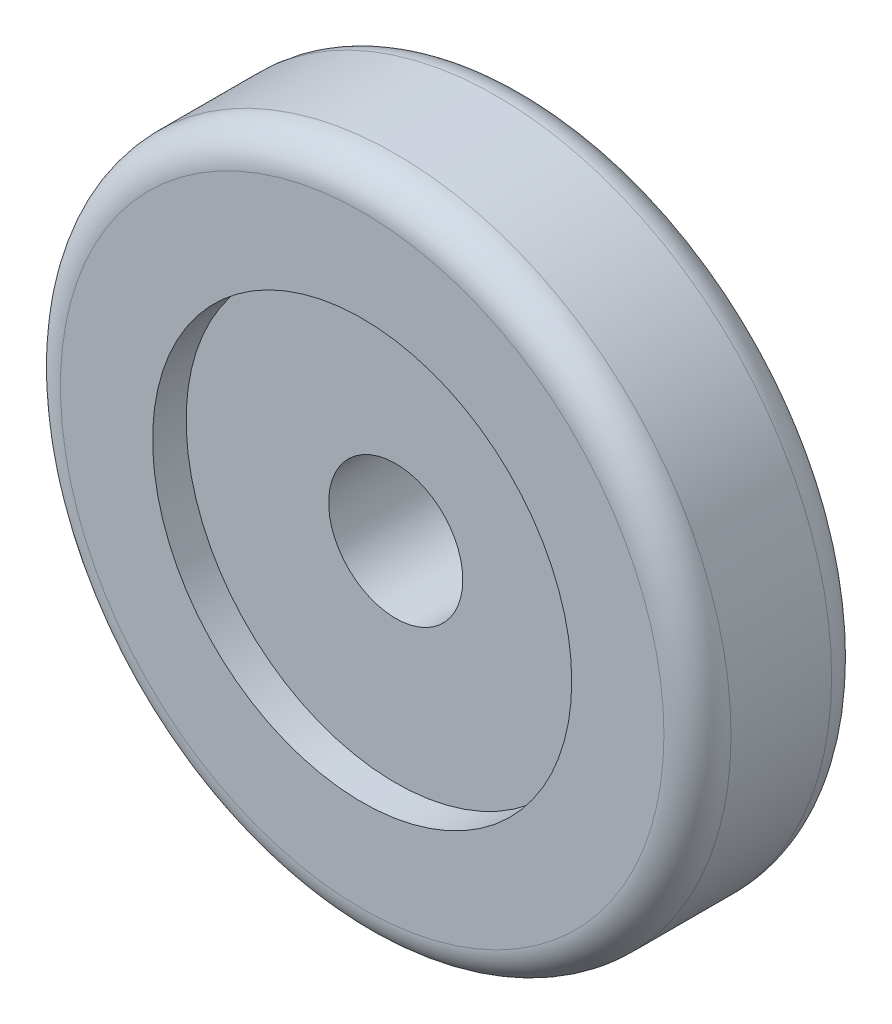
SolidWorks part; units mm, degrees
ref_plane "Front Plane" through (0, 0, 0) normal (0, 0, 1) x (1, 0, 0)
ref_plane "Top Plane" through (0, 0, 0) normal (0, 1, 0) x (1, 0, 0)
ref_plane "Right Plane" through (0, 0, 0) normal (1, 0, 0) x (0, 0, -1)
sketch "Sketch1" plane through (0, 0, 0) normal (0, 0, 1) x (1, 0, 0)
  circle A0 centre (0, 0) radius 20
  dimension "D1" = 40
extrude "Boss-Extrude1" add sketch "Sketch1" along normal blind 10
sketch "Sketch2" plane through (0, 0, 0) normal (0, 0, 1) x (1, 0, 0)
  circle A0 centre (0, 0) radius 4
  dimension "D1" = 8
extrude "Cut-Extrude1" cut sketch "Sketch2" along normal through all
sketch "Sketch3" plane through (0, 0, 10) normal (0, 0, 1) x (1, 0, 0)
  circle A0 centre (0, 0) radius 12.5
  dimension "D1" = 25
extrude "Cut-Extrude2" cut sketch "Sketch3" against normal blind 2
fillet "Fillet1" radius 2 2 edges at (20, 0, 0) (20, 0, 10)
